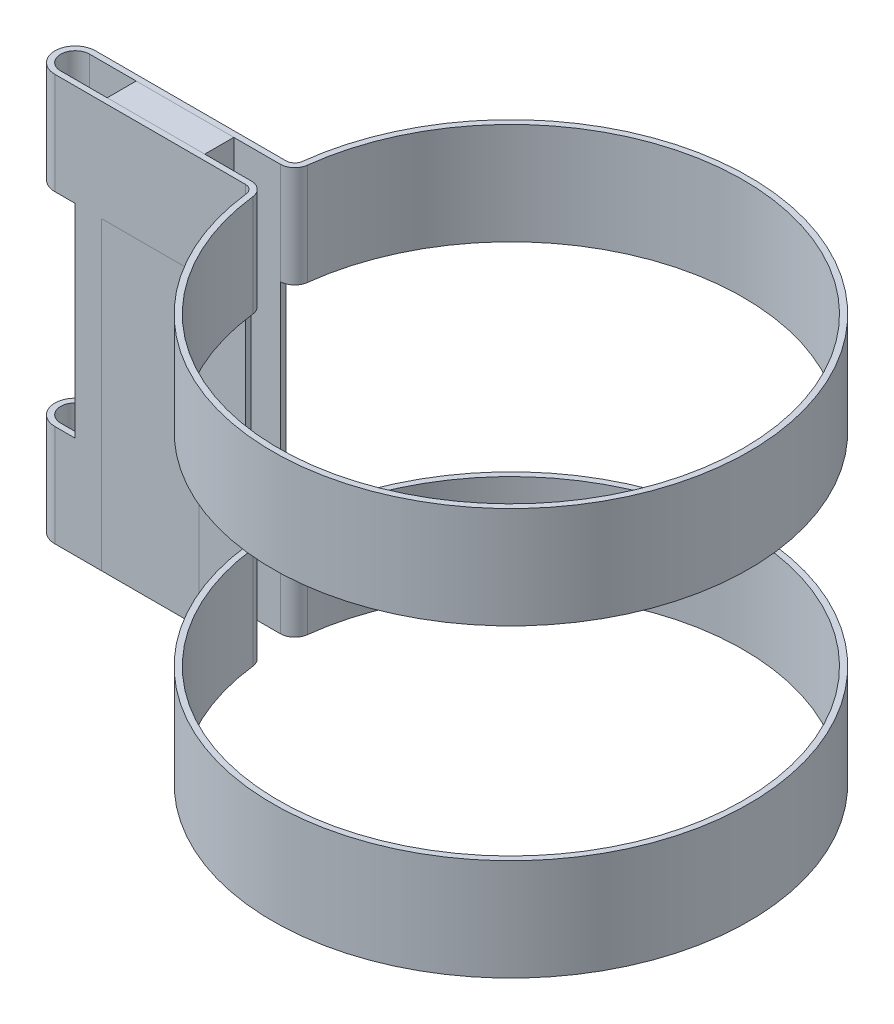
SolidWorks part; units mm, degrees
other "COLL.BOX-Boss-Extrude2"
ref_plane "Front Plane" through (0, 0, 0) normal (0, 0, 1) x (1, 0, 0)
ref_plane "Top Plane" through (0, 0, 0) normal (0, 1, 0) x (1, 0, 0)
ref_plane "Right Plane" through (0, 0, 0) normal (1, 0, 0) x (0, 0, -1)
sketch "Sketch1" plane through (0, 0, 0) normal (0, 1, 0) x (1, 0, 0)
  line L0 (-75, 3.5) -> (-42.2049, 3.5)
  line L1 (-75, 2.5) -> (-42.2049, 2.5)
  line L3 (-75, -2.5) -> (-42.2049, -2.5)
  line L5 (-75, -3.5) -> (-42.2049, -3.5)
  arc A0 (-39.7222, -4.7059) -> (-39.7222, 4.7059) centre (0, 0) ccw
  arc A1 (-75, 2.5) -> (-75, -2.5) centre (-75, 0) ccw
  arc A2 (-42.2049, 2.5) -> (-39.7222, 4.7059) centre (-42.2049, 5) ccw
  arc A3 (-39.7222, -4.7059) -> (-42.2049, -2.5) centre (-42.2049, -5) ccw
  arc A4 (-42.2049, 3.5) -> (-40.7153, 4.8235) centre (-42.2049, 5) ccw
  arc A5 (-40.7153, -4.8235) -> (-40.7153, 4.8235) centre (0, 0) ccw
  arc A6 (-40.7153, -4.8235) -> (-42.2049, -3.5) centre (-42.2049, -5) ccw
  arc A7 (-75, 3.5) -> (-75, -3.5) centre (-75, 0) ccw
  point P3 (-57.4609, 0)
  dimension "D1" = 80
  dimension "D3" = 5
  dimension "D5" = 5
  dimension "D6" = 5
  dimension "D2" = 5
  dimension "D4" = 75
  dimension "D7" = 1
extrude "Boss-Extrude1" add sketch "Sketch1" along normal blind 70
sketch "Sketch2" plane through (0, 0, 3.5) normal (0, 0, 1) x (1, 0, 0)
  line L0 (-75, 70) -> (-75, 0) construction
  line L1 (-78.5, 52.5) -> (-71.5, 52.5)
  line L2 (-78.5, 52.5) -> (-78.5, 17.5)
  line L3 (-78.5, 17.5) -> (-71.5, 17.5)
  line L4 (-71.5, 52.5) -> (-71.5, 17.5)
  line L5 (-78.5, 52.5) -> (-71.5, 17.5) construction
  line L6 (-78.5, 17.5) -> (-71.5, 52.5) construction
  line L7 (-75, 0) -> (-42.2049, 0) construction
  point P0 (-75, 35)
  dimension "D1" = 35
  dimension "D2" = 35
  dimension "D3" = 7
extrude "Cut-Extrude1" cut sketch "Sketch2" against normal up to surface (7 mm away) up to face at (-58.6024, 35, -3.5)
sketch "Sketch3" plane through (0, 0, 3.5) normal (0, 0, 1) x (1, 0, 0)
  line L0 (-42.2049, 70) -> (-42.2049, 0) construction
  line L1 (-42.2049, 52.5) -> (42.2049, 52.5)
  line L2 (-42.2049, 52.5) -> (-42.2049, 17.5)
  line L3 (-42.2049, 17.5) -> (42.2049, 17.5)
  line L4 (42.2049, 52.5) -> (42.2049, 17.5)
  line L5 (-42.2049, 52.5) -> (42.2049, 17.5) construction
  line L6 (-42.2049, 17.5) -> (42.2049, 52.5) construction
  line L7 (-40.7153, 0) -> (41, 0) construction
  point P0 (0, 35)
  dimension "D1" = 35
  dimension "D2" = 35
extrude "Cut-Extrude2" cut sketch "Sketch3" against normal through all and the other way through all
sketch "Sketch4" plane through (0, 70, 0) normal (0, 1, 0) x (1, 0, 0)
  line L0 (-42.2049, 3.5) -> (-75, 3.5) construction
  line L1 (-75, -3.5) -> (-42.2049, -3.5) construction
  line L2 (-67, 3.5) -> (-50.2049, 3.5)
  line L3 (-67, 3.5) -> (-67, -3.5)
  line L4 (-67, -3.5) -> (-50.2049, -3.5)
  line L5 (-50.2049, 3.5) -> (-50.2049, -3.5)
  arc A0 (-75, 3.5) -> (-75, -3.5) centre (-75, 0) ccw construction
  dimension "D1" = 8
  dimension "D2" = 8
extrude "Boss-Extrude2" add sketch "Sketch4" against normal up to vertex (70 mm away) separate body
